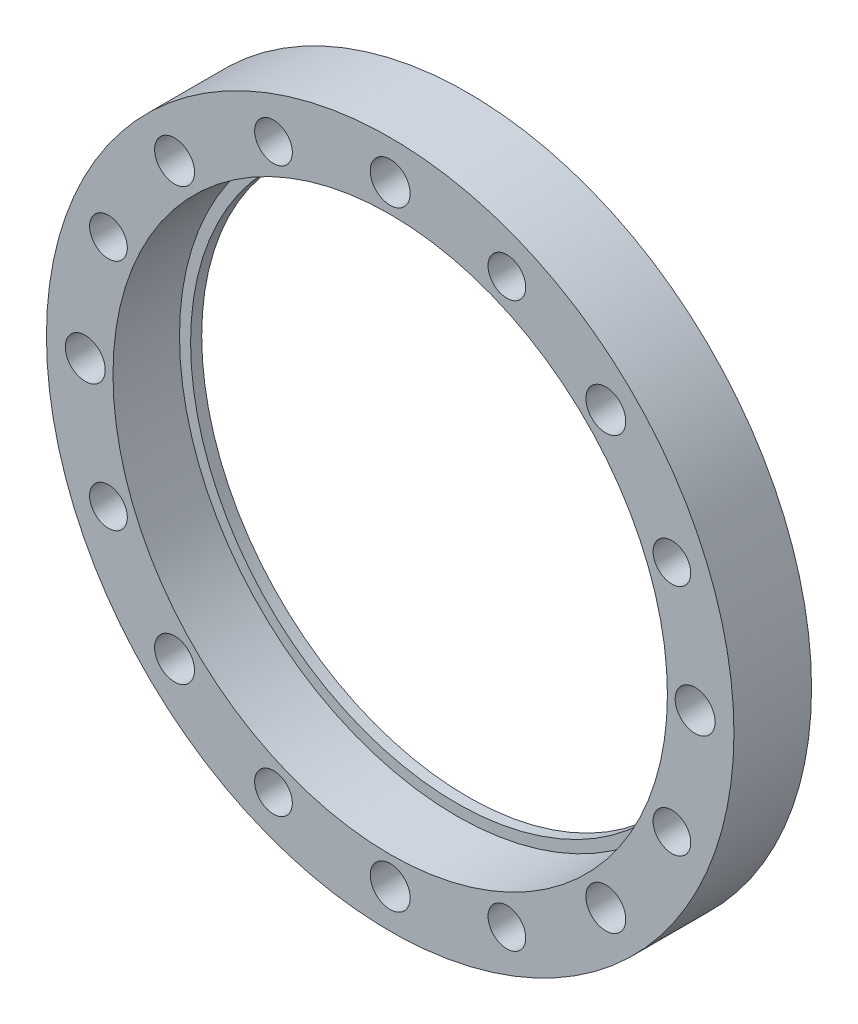
SolidWorks part; units mm, degrees
material "ABS"
ref_plane "正面" through (0, 0, 0) normal (0, 0, 1) x (1, 0, 0)
ref_plane "平面" through (0, 0, 0) normal (0, 1, 0) x (1, 0, 0)
ref_plane "右側面" through (0, 0, 0) normal (1, 0, 0) x (0, 0, -1)
sketch "ｽｹｯﾁ1" plane through (0, 0, 0) normal (0, 0, 1) x (1, 0, 0)
  circle A0 centre (0, 0) radius 31
  dimension "D1" = 62
extrude "ﾎﾞｽ - 押し出し1" add sketch "ｽｹｯﾁ1" along normal blind 6
sketch "ｽｹｯﾁ3" plane through (0, 0, 0) normal (0, 0, -1) x (-1, 0, 0)
  circle A0 centre (0, 0) radius 25
  dimension "D1" = 50
extrude "ｶｯﾄ - 押し出し1" cut sketch "ｽｹｯﾁ3" against normal through all
sketch "ｽｹｯﾁ5" plane through (0, 0, 0) normal (0, 0, -1) x (-1, 0, 0)
  circle A0 centre (0, 0) radius 24
  circle A1 centre (0, 0) radius 31
  circle A2 centre (0, 0) radius 31 construction
  circle A3 centre (0, 0) radius 25 construction
  dimension "D1" = 1
extrude "ﾎﾞｽ - 押し出し2" add sketch "ｽｹｯﾁ5" along normal blind 1
sketch "ｽｹｯﾁ6" plane through (0, 0, -1) normal (0, 0, -1) x (-1, 0, 0)
  circle A0 centre (0, 0) radius 27.5 construction
  circle A1 centre (0, 0) radius 31 construction
  dimension "D1" = 3.5
sketch "ｽｹｯﾁ9" plane through (0, 0, -1) normal (0, 0, -1) x (-1, 0, 0)
  line L1 (0, 41.0122) -> (41.0122, 0)
  line L2 (0, 41.0122) -> (-41.0122, 0)
  line L3 (-41.0122, 0) -> (0, -41.0122)
  line L4 (41.0122, 0) -> (0, -41.0122)
  line L5 (0, 41.0122) -> (0, -41.0122) construction
  line L6 (-41.0122, 0) -> (41.0122, 0) construction
  circle A0 centre (0, 0) radius 31 construction
  point P0 (0, 0)
  circle M15 centre (0, 0) radius 31
  dimension "D1" = 29
extrude "ｶｯﾄ - 押し出し2" [suppressed] cut sketch "ｽｹｯﾁ9" against normal through all contours L1 M15 | L3 M15
hole_wizard "M3 平皿頭ねじ用皿穴1" positions "ｽｹｯﾁ7" profile "ｽｹｯﾁ8" countersink size "M3" standard "JIS" end condition through all
sketch "ｽｹｯﾁ7" plane through (0, 0, -1) normal (0, 0, -1) x (-1, 0, 0)
  circle A0 centre (0, 0) radius 27.5 construction
  point P0 (0, 27.5)
sketch "ｽｹｯﾁ8" plane through (0, 27.5, -1) normal (1, 0, 0) x (0, 1, 0)
  line L0 (0, 0) -> (0, 7)
  line L1 (0, 7) -> (1.8, 7)
  line L2 (1.8, 7) -> (1.8, 1.35)
  line L3 (1.8, 1.35) -> (3.15, 0)
  line L5 (3.15, 0) -> (0, 0)
  line L6 (-1.8, 1.35) -> (-3.15, 0) construction
  line L11 (0, -6.35) -> (0, 107.95) construction
  dimension "通し穴の直径" = 3.6
  dimension "通し穴の深さ" = 7
  dimension "表面の皿穴の直径" = 6.3
  dimension "表面の皿穴の角度" = 90
pattern_circular "円形ﾊﾟﾀｰﾝ1" count 8 over 360 about axis through (0, 0, 0) along (0, 0, 1) of "M3 平皿頭ねじ用皿穴1"
hole_wizard "M3 すきま穴1" positions "ｽｹｯﾁ10" profile "ｽｹｯﾁ11" hole size "M3" standard "JIS" end condition through all
sketch "ｽｹｯﾁ10" plane through (0, 0, -1) normal (0, 0, -1) x (-1, 0, 0)
  arc A0 (-19.4454, 19.4454) -> (0, 27.5) centre (0, 0) cw construction
  point P0 (-10.5238, 25.4067)
sketch "ｽｹｯﾁ11" plane through (10.5238, 25.4067, -1) normal (1, 0, 0) x (0, 1, 0)
  line L0 (0, 0) -> (0, 7)
  line L1 (0, 7) -> (1.7, 7)
  line L2 (1.7, 7) -> (1.7, 0)
  line L5 (1.7, 0) -> (0, 0)
  line L11 (0, -6.35) -> (0, 107.95) construction
  dimension "通し穴の直径" = 3.4
  dimension "通し穴の深さ" = 7
pattern_circular "円形ﾊﾟﾀｰﾝ2" count 8 over 360 about axis through (0, 0, 0) along (0, 0, 1) of "M3 すきま穴1"
